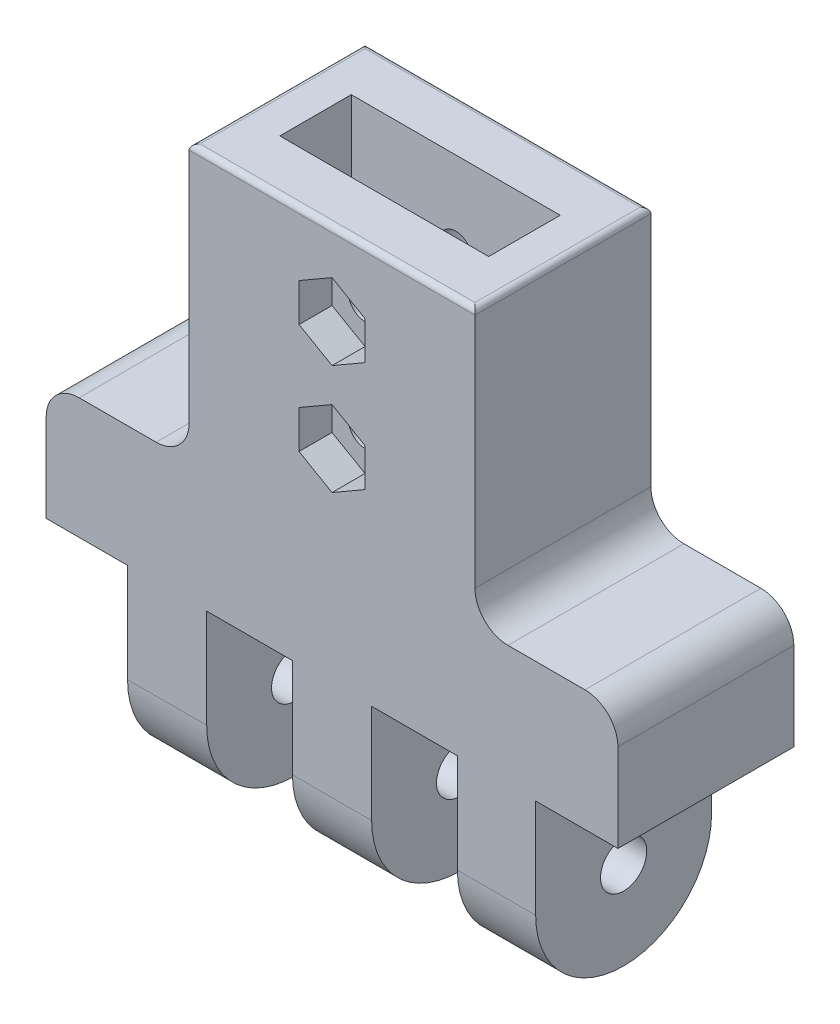
SolidWorks part; units mm, degrees
ref_plane "Front Plane" through (0, 0, 0) normal (0, 0, 1) x (1, 0, 0)
ref_plane "Top Plane" through (0, 0, 0) normal (0, 1, 0) x (1, 0, 0)
ref_plane "Right Plane" through (0, 0, 0) normal (1, 0, 0) x (0, 0, -1)
sketch "Sketch2" plane through (0, 0, 0) normal (1, 0, 0) x (0, 0, -1)
  line L2 (-8, 0) -> (-8, 20)
  line L3 (-8, 20) -> (8, 20)
  line L4 (8, 0) -> (8, 20)
  circle A0 centre (0, 0) radius 2.1
  arc A1 (-8, 0) -> (8, 0) centre (0, 0) ccw
  dimension "D1" = 16
  dimension "D2" = 4.2
  dimension "D3" = 20
extrude "Boss-Extrude1" add sketch "Sketch2" along normal mid plane 52
sketch "Sketch3" plane through (0, 0, 8) normal (0, 0, 1) x (1, 0, 0)
  line L0 (26, 0) -> (-26, 0) construction
  line L1 (-26, -9) -> (-18.6, -9)
  line L2 (-26, -9) -> (-26, 9)
  line L3 (-26, 9) -> (-18.6, 9)
  line L4 (-18.6, -9) -> (-18.6, 9)
  line L5 (-26, -9) -> (-18.6, 9) construction
  line L6 (-26, 9) -> (-18.6, -9) construction
  line L8 (-11.4, -9) -> (-3.6, -9)
  line L9 (-11.4, -9) -> (-11.4, 9)
  line L10 (-11.4, 9) -> (-3.6, 9)
  line L11 (-3.6, -9) -> (-3.6, 9)
  line L12 (-11.4, -9) -> (-3.6, 9) construction
  line L13 (-11.4, 9) -> (-3.6, -9) construction
  line L14 (3.6, -9) -> (11.4, -9)
  line L15 (3.6, -9) -> (3.6, 9)
  line L16 (3.6, 9) -> (11.4, 9)
  line L17 (11.4, -9) -> (11.4, 9)
  line L18 (3.6, -9) -> (11.4, 9) construction
  line L19 (3.6, 9) -> (11.4, -9) construction
  line L20 (-26, 20) -> (-26, 0) construction
  line L21 (26, 20) -> (26, 0) construction
  line L22 (18.519, -9) -> (26, -9)
  line L23 (18.519, -9) -> (18.519, 9)
  line L24 (18.519, 9) -> (26, 9)
  line L25 (26, -9) -> (26, 9)
  line L26 (18.519, -9) -> (26, 9) construction
  line L27 (18.519, 9) -> (26, -9) construction
  point P0 (-22.3, 0)
  point P7 (-7.5, 0)
  point P12 (7.5, 0)
  point P17 (-22.3, 9)
  point P20 (22.2595, 0)
  dimension "D1" = 9
  dimension "D4" = 7.2
  dimension "D6" = 7.2
  dimension "D2" = 7.8
  dimension "D3" = 14.6
extrude "Cut-Extrude1" cut sketch "Sketch3" against normal through all
ref_plane "Plane1" through (0, 20, 0) normal (0, 1, 0) x (1, 0, 0)
sketch "Sketch4" plane through (0, 20, 0) normal (0, 1, 0) x (1, 0, 0)
  line L0 (26, 8) -> (26, -8) construction
  line L1 (13, -8) -> (-13, -8)
  line L2 (13, -8) -> (13, 8)
  line L3 (13, 8) -> (-13, 8)
  line L4 (-13, -8) -> (-13, 8)
  line L5 (13, -8) -> (-13, 8) construction
  line L6 (13, 8) -> (-13, -8) construction
  line L8 (26, -8) -> (-26, -8) construction
  point P0 (0, 0)
  dimension "D1" = 26
  dimension "D2" = 16
  dimension "D3" = 26
extrude "Boss-Extrude2" add sketch "Sketch4" along normal blind 25
ref_plane "Plane2" through (0, 45, 0) normal (0, 1, 0) x (1, 0, 0)
sketch "Sketch5" plane through (0, 45, 0) normal (0, 1, 0) x (1, 0, 0)
  line L0 (13, -8) -> (13, 8) construction
  line L1 (-9.5, 3.25) -> (9.5, 3.25)
  line L2 (-9.5, 3.25) -> (-9.5, -3.25)
  line L3 (-9.5, -3.25) -> (9.5, -3.25)
  line L4 (9.5, 3.25) -> (9.5, -3.25)
  line L5 (-9.5, 3.25) -> (9.5, -3.25) construction
  line L6 (-9.5, -3.25) -> (9.5, 3.25) construction
  line L8 (-13, -8) -> (13, -8) construction
  line L10 (13, 8) -> (-13, 8) construction
  line L11 (13, -8) -> (13, 8) construction
  line L12 (-13, 8) -> (-13, -8) construction
  point P0 (0, 0)
  dimension "D1" = 19
  dimension "D2" = 13
  dimension "D3" = 6.5
  dimension "D4" = 8
  dimension "D5" = 4.75
extrude "Cut-Extrude2" cut sketch "Sketch5" against normal blind 25
fillet "Fillet2" radius 3 2 edges at (26, 20, 0) (-26, 20, 0)
sketch "Sketch6" plane through (0, 0, 0) normal (0, 0, 1) x (1, 0, 0)
  line L0 (9.5, 20) -> (9.5, 45) construction
  line L1 (-16.3932, 32.5) -> (15.2785, 32.5) construction
  line L2 (9.5, 20) -> (-9.5, 20) construction
  circle A0 centre (0, 37.5) radius 1.5
  circle A1 centre (0, 27.5) radius 1.5
  dimension "D1" = 3
  dimension "D2" = 9.5
  dimension "D3" = 10
  dimension "D4" = 5
  dimension "D5" = 12.5
extrude "Cut-Extrude3" cut sketch "Sketch6" against normal mid plane 25
fillet "Fillet3" radius 0.5 4 edges at (0, 45, 8) (13, 45, 0) (0, 45, -8) (-13, 45, 0)
fillet "Fillet4" radius 3 2 edges at (13, 20, 0) (-13, 20, 0)
ref_plane "Plane3" through (0, 0, 8) normal (0, 0, 1) x (1, 0, 0)
sketch "Sketch7" plane through (0, 0, 8) normal (0, 0, 1) x (1, 0, 0)
  line L1 (3, 35.7679) -> (3, 39.2321)
  line L2 (3, 39.2321) -> (0, 40.9641)
  line L3 (0, 40.9641) -> (-3, 39.2321)
  line L4 (-3, 39.2321) -> (-3, 35.7679)
  line L5 (-3, 35.7679) -> (0, 34.0359)
  line L6 (0, 34.0359) -> (3, 35.7679)
  line L7 (3, 25.7679) -> (3, 29.2321)
  line L8 (3, 29.2321) -> (0, 30.9641)
  line L9 (0, 30.9641) -> (-3, 29.2321)
  line L10 (-3, 29.2321) -> (-3, 25.7679)
  line L11 (-3, 25.7679) -> (0, 24.0359)
  line L12 (0, 24.0359) -> (3, 25.7679)
  circle A0 centre (0, 37.5) radius 3 construction
  circle A1 centre (0, 27.5) radius 3 construction
  circle A2 centre (0, 27.5) radius 1.5 construction
  dimension "D1" = 6
  dimension "D2" = 6
extrude "Cut-Extrude4" cut sketch "Sketch7" against normal blind 3
equation "\"hingewidth\"=7.2"
equation "\"fingerwidth\"=10.5"
equation "\"gapwidth\"=7.4"
equation "\"D4@Sketch3\"=\"hingewidth\""
equation "\"D6@Sketch3\"=\"hingewidth\""
